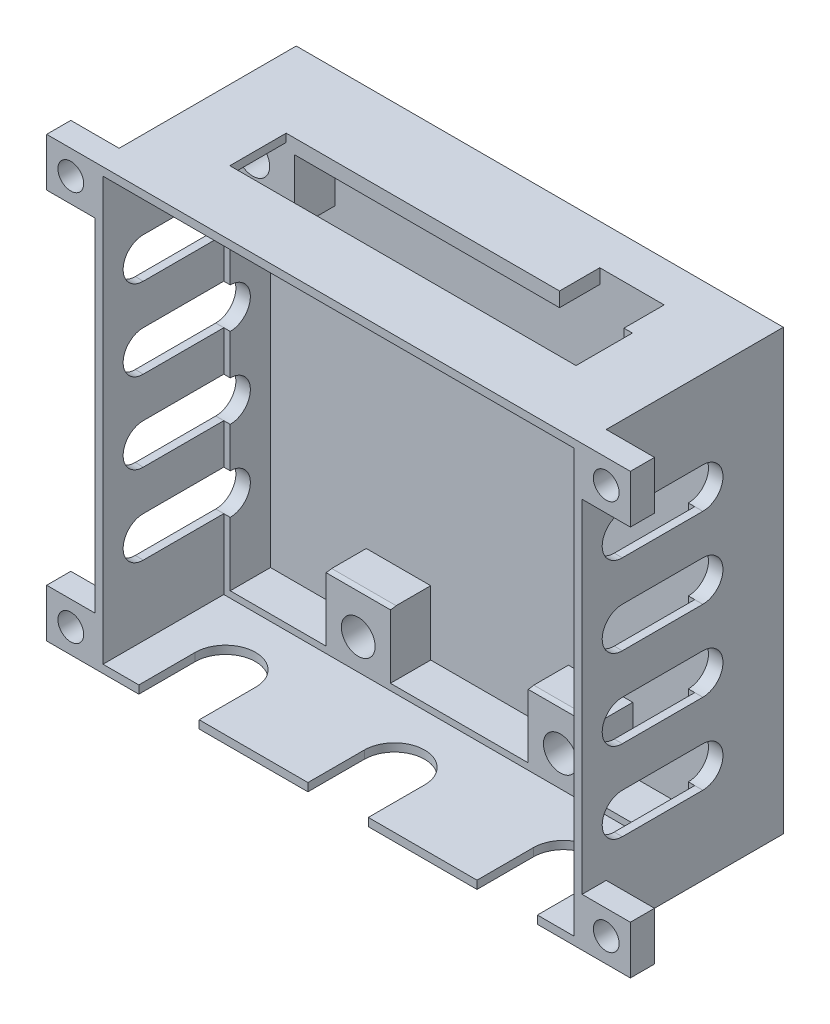
SolidWorks part; units mm, degrees
ref_plane "Alzado" through (0, 0, 0) normal (0, 0, 1) x (1, 0, 0)
ref_plane "Planta" through (0, 0, 0) normal (0, 1, 0) x (1, 0, 0)
ref_plane "Vista lateral" through (0, 0, 0) normal (1, 0, 0) x (0, 0, -1)
sketch "Croquis1" plane through (0, 0, 0) normal (0, 0, 1) x (1, 0, 0)
  line L1 (-73.5556, 30.3447) -> (-13.0556, 30.3447)
  line L2 (-73.5556, 30.3447) -> (-73.5556, -24.1553)
  line L3 (-73.5556, -24.1553) -> (-13.0556, -24.1553)
  line L4 (-13.0556, 30.3447) -> (-13.0556, -24.1553)
  dimension "D1" = 60.5
  dimension "D2" = 54.5
extrude "Saliente-Extruir1" add sketch "Croquis1" along normal blind 25
sketch "Croquis2" plane through (0, 0, 25) normal (0, 0, 1) x (1, 0, 0)
  line L0 (-13.0556, 30.3447) -> (-73.5556, 30.3447) construction
  line L1 (-71.7556, 28.5447) -> (-14.8556, 28.5447)
  line L2 (-71.7556, 28.5447) -> (-71.7556, -22.3553)
  line L3 (-71.7556, -22.3553) -> (-14.8556, -22.3553)
  line L4 (-14.8556, 28.5447) -> (-14.8556, -22.3553)
  line L5 (-13.0556, -24.1553) -> (-13.0556, 30.3447) construction
  line L6 (-73.5556, 30.3447) -> (-73.5556, -24.1553) construction
  line L7 (-73.5556, -24.1553) -> (-13.0556, -24.1553) construction
  dimension "D1" = 1.8
  dimension "D2" = 1.8
  dimension "D3" = 1.8
  dimension "D4" = 1.8
extrude "Cortar-Extruir1" cut sketch "Croquis2" against normal blind 15
sketch "Croquis3" plane through (0, 0, 10) normal (0, 0, 1) x (1, 0, 0)
  line L0 (-14.8556, 28.5447) -> (-71.7556, 28.5447) construction
  line L1 (-71.7556, 28.5447) -> (-71.7556, -22.3553) construction
  line L2 (-43.3056, 28.5447) -> (-43.3056, -22.3553) construction
  line L3 (-71.7556, -22.3553) -> (-14.8556, -22.3553) construction
  line L4 (-71.7556, 20.5447) -> (-71.7556, -22.3553)
  line L5 (-71.7556, 28.5447) -> (-63.7556, 28.5447) construction
  line L6 (-71.7556, 28.5447) -> (-71.7556, 20.5447) construction
  line L7 (-71.7556, 20.5447) -> (-63.7556, 20.5447)
  line L8 (-63.7556, 28.5447) -> (-63.7556, 20.5447)
  line L9 (-59.8556, -22.3553) -> (-51.8556, -22.3553) construction
  line L10 (-59.8556, -22.3553) -> (-59.8556, -14.3553)
  line L11 (-59.8556, -14.3553) -> (-51.8556, -14.3553)
  line L12 (-51.8556, -22.3553) -> (-51.8556, -14.3553)
  line L13 (-71.7556, -22.3553) -> (-59.8556, -22.3553)
  line L14 (-51.8556, -22.3553) -> (-34.7556, -22.3553)
  line L15 (-63.7556, 28.5447) -> (-22.8556, 28.5447)
  line L16 (-34.7556, -22.3553) -> (-34.7556, -14.3553)
  line L17 (-26.7556, -14.3553) -> (-34.7556, -14.3553)
  line L18 (-26.7556, -22.3553) -> (-26.7556, -14.3553)
  line L19 (-14.8556, -22.3553) -> (-26.7556, -22.3553)
  line L20 (-14.8556, 20.5447) -> (-14.8556, -22.3553)
  line L21 (-14.8556, 20.5447) -> (-22.8556, 20.5447)
  line L22 (-22.8556, 28.5447) -> (-22.8556, 20.5447)
  circle A0 centre (-68.9556, 25.7447) radius 2.1
  circle A1 centre (-55.8556, -19.3553) radius 2.1
  circle A2 centre (-30.7556, -19.3553) radius 2.1
  circle A3 centre (-17.6556, 25.7447) radius 2.1
  point P21 (-55.8556, -14.3553)
  dimension "D1" = 4.2
  dimension "D3" = 2.8
  dimension "D4" = 4.2
  dimension "D5" = 3
  dimension "D6" = 15.9
  dimension "D2" = 2.8
  dimension "D7" = 8
  dimension "D8" = 8
  dimension "D9" = 8
  dimension "D10" = 8
extrude "Cortar-Extruir2" cut sketch "Croquis3" against normal blind 5
sketch "Croquis5" plane through (0, -22.3553, 0) normal (0, 1, 0) x (1, 0, 0)
  line L0 (-34.7556, -10) -> (-26.7556, -10) construction
  line L1 (-14.8556, -5) -> (-14.8556, -25) construction
  line L2 (-18.6056, -18) -> (-18.6056, -25)
  line L3 (-71.7556, -25) -> (-14.8556, -25) construction
  line L4 (-18.6056, -25) -> (-26.1056, -25)
  line L5 (-26.1056, -25) -> (-26.1056, -18)
  line L6 (-39.6056, -18) -> (-39.6056, -25)
  line L7 (-39.6056, -25) -> (-47.1056, -25)
  line L8 (-47.1056, -25) -> (-47.1056, -18)
  line L9 (-60.6056, -18) -> (-60.6056, -25)
  line L10 (-60.6056, -25) -> (-68.1056, -25)
  line L11 (-68.1056, -25) -> (-68.1056, -18)
  arc A0 (-18.6056, -18) -> (-26.1056, -18) centre (-22.3556, -18) ccw
  arc A3 (-39.6056, -18) -> (-47.1056, -18) centre (-43.3556, -18) ccw
  arc A4 (-60.6056, -18) -> (-68.1056, -18) centre (-64.3556, -18) ccw
  dimension "D1" = 7.5
  dimension "D2" = 8
  dimension "D3" = 7.5
  dimension "D4" = 3
extrude "Cortar-Extruir3" cut sketch "Croquis5" against normal blind 5
sketch "Croquis6" plane through (0, 28.5447, 0) normal (0, -1, 0) x (1, 0, 0)
  line L0 (-14.8556, 10) -> (-22.8556, 10) construction
  line L1 (-64.8056, 17) -> (-21.8056, 17)
  line L2 (-64.8056, 17) -> (-64.8056, 10)
  line L3 (-64.8056, 10) -> (-30.8556, 10)
  line L4 (-21.8056, 17) -> (-21.8056, 10)
  line L5 (-14.8556, 25) -> (-71.7556, 25) construction
  line L6 (-63.7556, 10) -> (-71.7556, 10) construction
  line L8 (-22.8556, 5) -> (-63.7556, 5) construction
  line L10 (-22.8556, 10) -> (-22.8556, 5)
  line L11 (-22.8556, 5) -> (-30.8556, 5)
  line L12 (-30.8556, 10) -> (-30.8556, 5)
  line L13 (-22.8556, 10) -> (-21.8056, 10)
  point P6 (-43.3056, 17)
  point P9 (-43.3056, 25)
  dimension "D1" = 7
  dimension "D2" = 43
  dimension "D3" = 8
extrude "Cortar-Extruir4" cut sketch "Croquis6" against normal up to vertex (1.8 mm away)
sketch "Croquis9" plane through (-71.7556, 0, 0) normal (1, 0, 0) x (0, 0, -1)
  line L0 (-5, 20.5447) -> (-10, 20.5447) construction
  line L1 (-10, 20.5447) -> (-20, 20.5447)
  line L3 (-10, 15.5447) -> (-20, 15.5447)
  line L7 (-5, 20.5447) -> (-5, -22.3553) construction
  line L8 (-25, 28.5447) -> (-25, -22.3553) construction
  line L9 (-10, 10.5447) -> (-20, 10.5447)
  line L10 (-10, 5.5447) -> (-20, 5.5447)
  line L11 (-10, 0.5447) -> (-20, 0.5447)
  line L12 (-10, -4.4553) -> (-20, -4.4553)
  line L13 (-10, -9.4553) -> (-20, -9.4553)
  line L14 (-10, -14.4553) -> (-20, -14.4553)
  arc A0 (-20, 20.5447) -> (-20, 15.5447) centre (-20, 18.0447) ccw
  arc A1 (-10, 15.5447) -> (-10, 20.5447) centre (-10, 18.0447) ccw
  arc A2 (-20, 10.5447) -> (-20, 5.5447) centre (-20, 8.0447) ccw
  arc A3 (-10, 5.5447) -> (-10, 10.5447) centre (-10, 8.0447) ccw
  arc A4 (-20, 0.5447) -> (-20, -4.4553) centre (-20, -1.9553) ccw
  arc A5 (-10, -4.4553) -> (-10, 0.5447) centre (-10, -1.9553) ccw
  arc A6 (-20, -9.4553) -> (-20, -14.4553) centre (-20, -11.9553) ccw
  arc A7 (-10, -14.4553) -> (-10, -9.4553) centre (-10, -11.9553) ccw
  dimension "D1" = 5
  dimension "D2" = 5
  dimension "D3" = 5
  dimension "D4" = 4
extrude "Cortar-Extruir6" cut sketch "Croquis9" against normal up to vertex and the other way up to surface
sketch "Croquis10" plane through (0, 0, 25) normal (0, 0, 1) x (1, 0, 0)
  line L0 (-43.3056, 30.3447) -> (-43.3056, -24.1553) construction
  line L1 (-73.5556, 30.3447) -> (-79.5556, 30.3447)
  line L2 (-73.5556, 30.3447) -> (-73.5556, 24.3447)
  line L3 (-73.5556, 24.3447) -> (-79.5556, 24.3447)
  line L4 (-79.5556, 30.3447) -> (-79.5556, 24.3447)
  line L5 (-13.0556, 30.3447) -> (-73.5556, 30.3447) construction
  line L6 (-7.0556, 30.3447) -> (-7.0556, 24.3447)
  line L7 (-13.0556, 24.3447) -> (-7.0556, 24.3447)
  line L8 (-13.0556, 30.3447) -> (-13.0556, 24.3447)
  line L9 (-13.0556, 30.3447) -> (-7.0556, 30.3447)
  line L10 (-73.5556, 3.0947) -> (-13.0556, 3.0947) construction
  line L11 (-73.5556, 30.3447) -> (-73.5556, -24.1553) construction
  line L12 (-13.0556, -24.1553) -> (-13.0556, 30.3447) construction
  line L13 (-13.0556, -24.1553) -> (-7.0556, -24.1553)
  line L14 (-13.0556, -24.1553) -> (-13.0556, -18.1553)
  line L15 (-13.0556, -18.1553) -> (-7.0556, -18.1553)
  line L16 (-7.0556, -24.1553) -> (-7.0556, -18.1553)
  line L17 (-79.5556, -24.1553) -> (-79.5556, -18.1553)
  line L18 (-73.5556, -18.1553) -> (-79.5556, -18.1553)
  line L19 (-73.5556, -24.1553) -> (-73.5556, -18.1553)
  line L20 (-73.5556, -24.1553) -> (-79.5556, -24.1553)
  circle A0 centre (-76.5556, 27.3447) radius 1.6
  circle A1 centre (-10.0556, 27.3447) radius 1.6
  circle A2 centre (-10.0556, -21.1553) radius 1.6
  circle A3 centre (-76.5556, -21.1553) radius 1.6
  dimension "D1" = 6
  dimension "D2" = 6
extrude "Saliente-Extruir2" add sketch "Croquis10" against normal blind 3
sketch "Croquis11" plane through (0, 0, 25) normal (0, 0, 1) x (1, 0, 0)
  line L10 (-14.8556, 28.5447) -> (-71.7556, 28.5447) construction
  line L11 (-72.5556, 29.3447) -> (-14.0556, 29.3447)
  line L12 (-72.5556, 29.3447) -> (-72.5556, -23.1553)
  line L13 (-72.5556, -23.1553) -> (-14.0556, -23.1553)
  line L14 (-14.0556, 29.3447) -> (-14.0556, -23.1553)
  line L15 (-71.7556, 28.5447) -> (-71.7556, -22.3553) construction
  line L16 (-14.8556, -22.3553) -> (-14.8556, 28.5447) construction
  line L17 (-18.6056, -22.3553) -> (-14.8556, -22.3553) construction
  dimension "D1" = 0.8
  dimension "D2" = 0.8
  dimension "D3" = 0.8
  dimension "D4" = 0.8
extrude "Cortar-Extruir7" cut sketch "Croquis11" against normal up to vertex (15 mm away)
